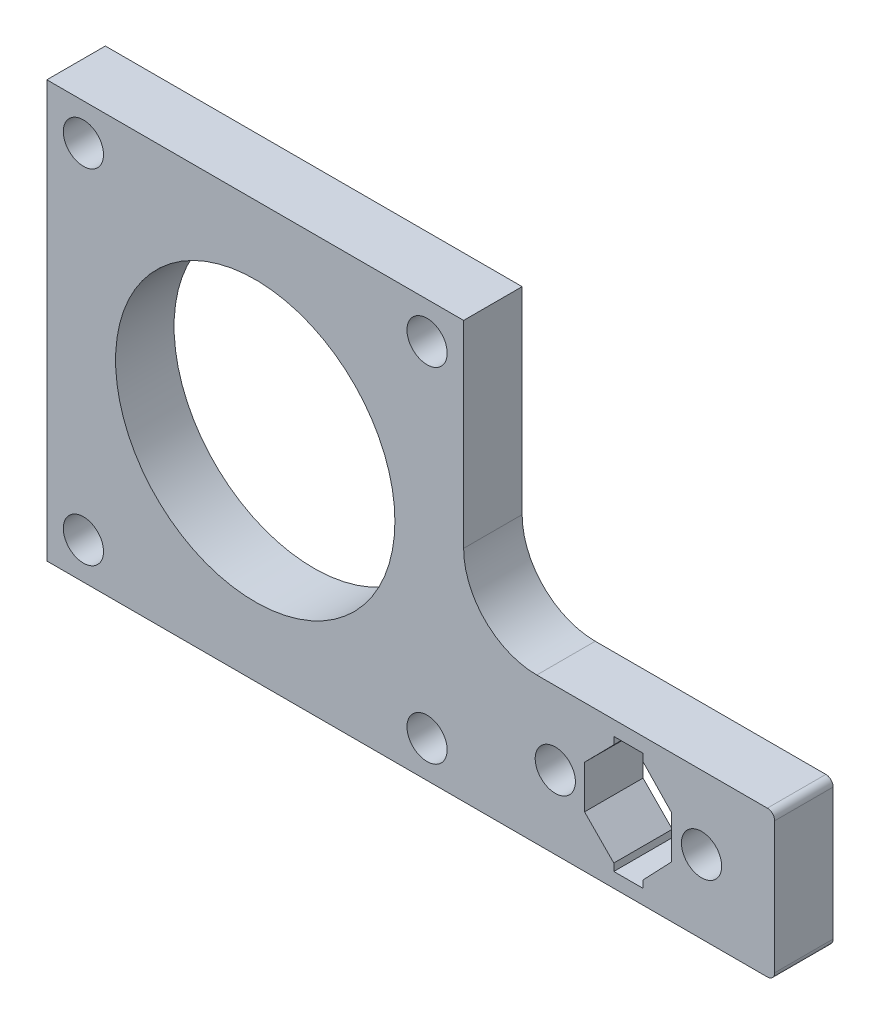
SolidWorks part; units mm, degrees
material "ABS"
ref_plane "Front Plane" through (0, 0, 0) normal (0, 0, 1) x (1, 0, 0)
ref_plane "Top Plane" through (0, 0, 0) normal (0, 1, 0) x (1, 0, 0)
ref_plane "Right Plane" through (0, 0, 0) normal (1, 0, 0) x (0, 0, -1)
sketch "Stepper Plate Sketch" plane through (0, 0, 0) normal (0, 0, 1) x (1, 0, 0)
  line L0 (-10, -39) -> (10, -39) construction
  line L1 (-79.5368, 8) -> (-22.5368, 8)
  line L2 (-79.5368, 8) -> (-79.5368, -49)
  line L3 (-79.5368, -49) -> (-22.5368, -49)
  line L4 (-22.5368, 8) -> (-22.5368, -49)
  line L5 (-79.5368, 8) -> (-22.5368, -49) construction
  line L6 (-79.5368, -49) -> (-22.5368, 8) construction
  line L7 (-20, -49) -> (20, -49)
  line L8 (-20, -49) -> (-20, -29)
  line L9 (-20, -29) -> (20, -29)
  line L10 (20, -49) -> (20, -29)
  line L11 (-20, -49) -> (20, -29) construction
  line L12 (-20, -29) -> (20, -49) construction
  line L13 (-74.5368, 3) -> (-27.5368, 3) construction
  line L14 (-74.5368, 3) -> (-74.5368, -44) construction
  line L15 (-74.5368, -44) -> (-27.5368, -44) construction
  line L16 (-27.5368, 3) -> (-27.5368, -44) construction
  line L17 (0, 0) -> (-51.0368, -20.5) construction
  line L18 (-20, -29) -> (-22.5368, -29)
  line L19 (-20, -49) -> (-22.5368, -49)
  line L20 (-2, -31) -> (2, -31)
  line L21 (2, -31) -> (2, -32)
  line L22 (2, -32) -> (5.88, -36.06)
  line L23 (5.88, -36.06) -> (5.88, -41.94)
  line L24 (5.88, -41.94) -> (2, -46)
  line L25 (2, -46) -> (2, -47)
  line L26 (2, -47) -> (-2, -47)
  line L27 (-2, -47) -> (-2, -46)
  line L28 (-2, -46) -> (-6, -41.94)
  line L29 (-6, -41.94) -> (-6, -36.06)
  line L30 (-6, -36.06) -> (-2, -32)
  line L31 (-2, -32) -> (-2, -31)
  line L32 (2, -32) -> (2, -46) construction
  line L33 (-2, -46) -> (-2, -32) construction
  line L34 (2, -32) -> (-2, -32)
  line L35 (-2, -46) -> (2, -46)
  circle A0 centre (0, 0) radius 10 construction
  circle A1 centre (-51.0368, -20.5) radius 19.1
  point P0 (-51.0368, -20.5)
  point P8 (0, -39)
  point P22 (0, -39)
  point P34 (0, -47)
  point P36 (-6, -39)
  point P37 (5.88, -39)
  point P38 (0.9111, -47.4708)
  point P39 (4.1618, -36.06)
  point P40 (5.8561, -36.072)
  point P41 (-6, -36)
  point P42 (2, -31.2967)
  dimension "D2" = 20
  dimension "D4" = 38.2
  dimension "D1" = 29
  dimension "D3" = 20
  dimension "Bracket Width" = 40
  dimension "Stepper_Width" = 57
  dimension "Stepper_BoltDistance" = 47
  dimension "D5" = 20
  dimension "X_CenterDistance" = 55
  dimension "D6" = 1
  dimension "D7" = 5.88
  dimension "D8" = 4
  dimension "D9" = 4
  dimension "D10" = 8
extrude "Plate Boss-Extrude" add sketch "Stepper Plate Sketch" against normal blind 8 contours L4 L1 L2 L3 A1 | L7 L10 L9 L8 | L19 L8 L18 L4
fillet "Fillet1" radius 10 1 edges at (-22.5368, -29, -4)
fillet "Fillet2" radius 1 2 edges at (20, -49, -4) (20, -29, -4)
hole_wizard "M5 Clearance Hole1" positions "Sketch2" profile "Sketch3" hole size "M5" standard "ANSI Metric" end condition through all
sketch "Sketch2" plane through (0, 0, 0) normal (0, 0, 1) x (1, 0, 0)
  point P0 (-74.5368, 3)
  point P3 (-74.5368, -44)
  point P6 (-27.5368, -44)
  point P9 (-27.5368, 3)
  point P12 (-10, -39)
  point P15 (10, -39)
sketch "Sketch3" plane through (-74.5368, 3, 0) normal (1, 0, 0) x (0, -1, 0)
  line L0 (0, 0) -> (0, 8)
  line L1 (0, 8) -> (2.75, 8)
  line L2 (2.75, 8) -> (2.75, 0)
  line L5 (2.75, 0) -> (0, 0)
  line L11 (0, -6.35) -> (0, 107.95) construction
  dimension "Thru Hole Dia." = 5.5
  dimension "Thru Hole Depth" = 8
equation "\"ExtrusionStandard\"= 20mm'Size of extrusion used for framing"
equation "\"BaseExtrusionFrameWidth\"= 60mm"
equation "\"BaseExtrusionFrameHeight\"= 20mm"
equation "\"PlateThickness\"= 15mm"
equation "\"RailHeight\"=13"
equation "\"WallThickness\"= 3mm"
equation "\"ShaftDiameter\"= 20mm"
equation "\"ShaftClearance\"= 1mm"
equation "\"PlainBearingBoltCircleDiameter\"= ( \"ShaftDiameter\" / 2 ) + \"ShaftClearance\" + \"WallThickness\" + 5mm"
equation "\"PlainBearingBoltcount\"=5"
equation "\"ThrustBearingOD\"= 35mm"
equation "\"ThrustBearingID\"= 20mm"
equation "\"ThrustBearingThickness\"= 10mm"
equation "\"RearCollarOD\"= 32mm"
equation "\"RearCollarID\"= 20mm"
equation "\"RearCollarThickness\"= 14mm"
equation "\"LeadScrewDiameter\"= 6.35mm"
equation "\"LeadScrewHeight\"= 10mm'Height of Lead screw from bottom of gantry extrusion"
equation "\"LeadScrewNut_FlangeOD\"= 25mm'OD of the lead screw nut flange"
equation "\"LeadScrewNut_BoltCircleDiameter\"= 19mm"
equation "\"LeadScrewNut_BoltCount\"= 6"
equation "\"ShaftOffset_BaseThickness\"= 6mm + \"WallThickness\""
equation "\"PillowHeight\"= \"ShaftOffset_BaseThickness\" + \"ExtrusionStandard\""
equation "\"D1@Stepper Plate Sketch\" = \"PillowHeight\""
equation "\"D2@Stepper Plate Sketch\" = \"ShaftDiameter\""
equation "\"D3@Stepper Plate Sketch\" = \"ExtrusionStandard\""
equation "\"Bracket Width@Stepper Plate Sketch\" = \"ExtrusionStandard\" * 2"
equation "\"D5@Stepper Plate Sketch\" = \"ExtrusionStandard\""
equation "\"D1@Plate Boss-Extrude\" = 5mm + \"WallThickness\""
